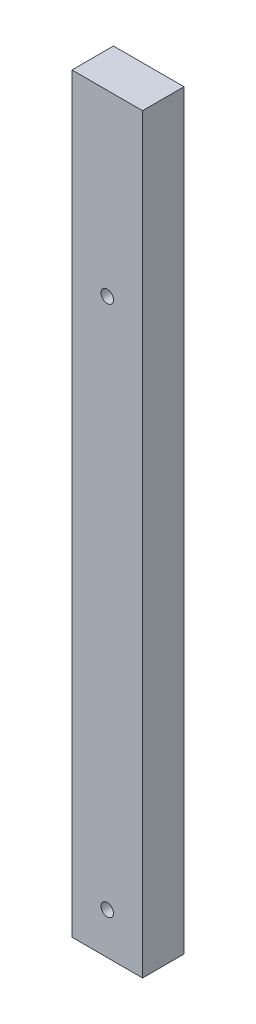
SolidWorks part; units mm, degrees
ref_plane "Plan de face" through (0, 0, 0) normal (0, 0, 1) x (1, 0, 0)
ref_plane "Plan de dessus" through (0, 0, 0) normal (0, 1, 0) x (1, 0, 0)
ref_plane "Plan de droite" through (0, 0, 0) normal (1, 0, 0) x (0, 0, -1)
sketch "Esquisse1" plane through (0, 0, 0) normal (0, 0, 1) x (1, 0, 0)
  line L1 (-8.5, 90.5) -> (8.5, 90.5)
  line L2 (-8.5, 90.5) -> (-8.5, -90.5)
  line L3 (-8.5, -90.5) -> (8.5, -90.5)
  line L4 (8.5, 90.5) -> (8.5, -90.5)
  dimension "D1" = 181
  dimension "D2" = 17
  dimension "D3" = 8.5
  dimension "D4" = 90.5
extrude "Boss.-Extru.1" add sketch "Esquisse1" along normal blind 10
sketch "Esquisse2" plane through (0, 0, 10) normal (0, 0, 1) x (1, 0, 0)
  line L0 (-8.5, -90.5) -> (8.5, -90.5) construction
  line L2 (8.5, -90.5) -> (8.5, 90.5) construction
  circle A0 centre (0, 47.5) radius 1.5
  circle A1 centre (0, -80.5) radius 1.5
  dimension "D1" = 3
  dimension "D2" = 3
  dimension "D3" = 128
  dimension "D4" = 10
  dimension "D5" = 8.5
  dimension "D6" = 8.5
extrude "Enlèv. mat.-Extru.1" cut sketch "Esquisse2" against normal blind 5
sketch "Esquisse4" plane through (0, 0, 0) normal (0, 0, -1) x (-1, 0, 0)
  line L0 (8.5, -90.5) -> (-8.5, -90.5) construction
  line L1 (8.5, 90.5) -> (8.5, -90.5) construction
  circle A0 centre (0, 14.5) radius 1.5
  circle A1 centre (0, -40.5) radius 1.5
  point P4 (0, -90.5)
  dimension "D1" = 3
  dimension "D2" = 3
  dimension "D5" = 8.5
  dimension "D3" = 50
  dimension "D4" = 55
  dimension "D6" = 8.5
extrude "Enlèv. mat.-Extru.2" cut sketch "Esquisse4" against normal blind 5
equation "\"D3@Esquisse1\"=\"D2@Esquisse1\"/2"
equation "\"D4@Esquisse1\"=\"D1@Esquisse1\"/2"
